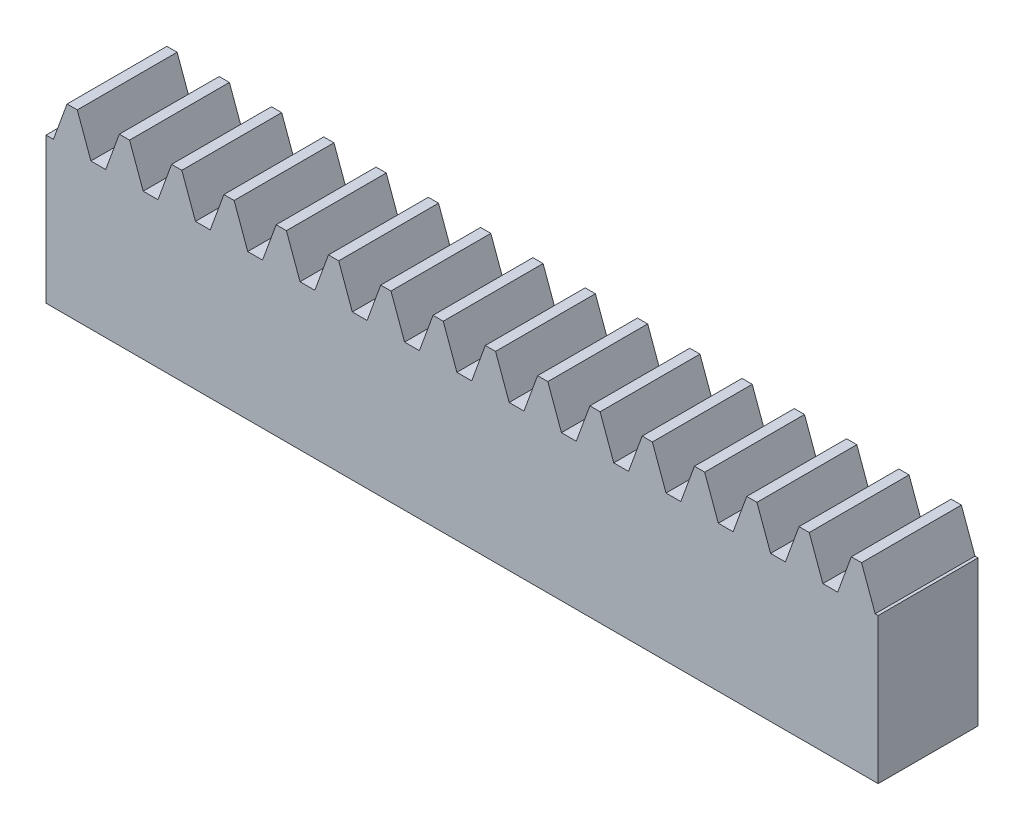
SolidWorks part; units mm, degrees
extrude "Blank" add sketch "BlankSke" against normal blind 6
sketch "BlankSke" plane through (0, 0, 0) normal (0, 0, 1) x (1, 0, 0)
  line L1 (0, 0) -> (50, 0)
  line L2 (0, 0) -> (0, 11)
  line L3 (0, 11) -> (50, 11)
  line L4 (50, 0) -> (50, 11)
  dimension "Length" = 50
  dimension "Blank_height" = 11
ref_plane "Plane1" through (0, 0, 0) normal (0, 0, 1) x (1, 0, 0)
ref_plane "Plane2" through (0, 0, 0) normal (0, 1, 0) x (1, 0, 0)
ref_plane "Plane3" through (0, 0, 0) normal (1, 0, 0) x (0, 0, -1)
sketch "HoldingSke" plane through (0, 0, 0) normal (0, 1, 0) x (1, 0, 0)
  line L0 (0, 0) -> (0.1392, 0.9903)
  line L1 (-15, 0) -> (100, 0) construction
  line L2 (0, 0) -> (-2.1039, 2.3779)
  line L3 (0, 0) -> (-11.863, 4.5341)
  line L4 (0, 0) -> (8.2587, 2.5249)
  line L5 (0, 0) -> (-23.7986, -8.8762)
  line L6 (0, 0) -> (-10.5278, -7.1032)
  line L9 (-71.009, 38.7566) -> (-24.0243, 55.8576)
  line L10 (-76.2, 3.3779) -> (-66.2, 3.3779)
  line L11 (0, 0) -> (-6, 0)
  line L12 (-76.2, 101.6) -> (-76.162, 101.6)
  line L13 (24.9733, 27.94) -> (52.9518, 28.4284)
  line L14 (24.9733, 27.94) -> (24.9743, 27.94)
  line L15 (24.9733, 27.94) -> (100.4006, 29.5858)
  circle A0 centre (0, 0) radius 19.05
  circle A1 centre (0, 0) radius 5
  circle A2 centre (0, 0) radius 12.7
  dimension "MPH" = 10
  dimension "Diameter" = 38.1
  dimension "Num_teeth" = 17
  dimension "Pitch" = 1
  dimension "Show_teeth" = 998
  dimension "Thickness" = 12.7
  dimension "Ap" = 20
  dimension "Pitch_height" = 10
  dimension "Width" = 6
  dimension "Backlash" = 0.038
  dimension "Addendum_fac" = 1
  dimension "Dedendum_fac" = 1.25
  dimension "Clearance_fac" = 0.25
  dimension "Dedendum_add" = 0.001
  dimension "Length" = 50
  dimension "Module" = 1
sketch "TooCutSkeIll" plane through (0, 0, 0) normal (0, 0, 1) x (1, 0, 0)
  line L0 (-1.2538, 10.9737) -> (-0.5045, 8.9152)
  line L1 (-0.2687, 8.75) -> (0.2687, 8.75)
  line L2 (0.5045, 8.9152) -> (1.2538, 10.9737)
  line L3 (50, 11) -> (0, 11) construction
  line L4 (0, 0) -> (0, 64.897) construction
  line L5 (-13.208, 10) -> (12.954, 10) construction
  line L6 (0, 0) -> (50, 0) construction
  line L7 (0.8994, 10) -> (0.8994, 48.7463) construction
  line L8 (-0.8994, 10) -> (-0.8994, 48.7463) construction
  line L9 (1.2914, 11) -> (1.2914, 11.0254)
  line L10 (-1.2914, 11) -> (-1.2914, 11.0254)
  line L11 (-1.2914, 11.0254) -> (1.2914, 11.0254)
  arc A0 (0.2687, 8.75) -> (0.5045, 8.9152) centre (0.2687, 9.001) ccw
  arc A1 (-0.5045, 8.9152) -> (-0.2687, 8.75) centre (-0.2687, 9.001) ccw
  arc A2 (1.2914, 11) -> (1.2538, 10.9737) centre (1.2914, 10.96) ccw
  arc A3 (-1.2538, 10.9737) -> (-1.2914, 11) centre (-1.2914, 10.96) ccw
  dimension "Pitch_height" = 10
  dimension "Addendum_plus" = 1.0254
  dimension "Pressure_angle" = 20
  dimension "Gap_width" = 1.7988
  dimension "Dedendum" = 1.25
extrude "ToothCutIll" [suppressed] cut sketch "TooCutSkeIll" against normal through all
sketch "TooCutSkeSim" plane through (0, 0, 0) normal (0, 0, 1) x (1, 0, 0)
  line L0 (0.4444, 8.75) -> (-0.4444, 8.75)
  line L1 (1.2726, 11.0254) -> (0.4444, 8.75)
  line L2 (0, 17.4625) -> (0, 53.467) construction
  line L3 (1.2726, 11.0254) -> (-1.2726, 11.0254)
  line L6 (-1.2726, 11.0254) -> (-0.4444, 8.75)
  line L9 (-0.8994, 10) -> (0.8994, 10) construction
  line L10 (0, 0) -> (50, 0) construction
  line L11 (0.8994, 10) -> (0.8994, 53.467) construction
  line L12 (-0.8994, 10) -> (-0.8994, 53.467) construction
  dimension "Pitch_height" = 10
  dimension "Addendum_plus" = 1.0254
  dimension "Pressure_angle" = 20
  dimension "Gap_width" = 1.7988
  dimension "Dedendum" = 1.25
extrude "ToothCutSim" cut sketch "TooCutSkeSim" against normal through all
pattern_linear "TeethCuts" count 17 spacing 3.1416 along (1, 0, 0) of "ToothCutIll", "ToothCutSim"
equation "' \"Module@HoldingSke\" = 6.35"
equation "' \"Num_teeth@HoldingSke\" = 12"
equation "' \"Ap@HoldingSke\" =  20"
equation "' \"Ap@HoldingSke\" = 20"
equation "' \"Width@HoldingSke\" = 0.25 * 25.4"
equation "' \"Show_teeth@HoldingSke\" = 500"
equation "' \"Backlash@HoldingSke\" = 0.009 * 25.4"
equation "' \"Addendum_fac@HoldingSke\" = 1.0"
equation "' \"Dedendum_fac@HoldingSke\" = 1.25"
equation "' \"Dedendum_add@HoldingSke\" = 0.00005 * 25.4"
equation "' \"Clearance_fac@HoldingSke\" = 0.25"
equation "' \"Pitch_height@HoldingSke\" = 1 * 25.4"
equation "' \"Length@HoldingSke\" = 4.71 * 25.4"
equation "\"Pitch@HoldingSke\" = 1 / \"Module@HoldingSke\""
equation "\"MPH@HoldingSke\" = \"Dedendum_fac@HoldingSke\" / \"Pitch@HoldingSke\" + 2 * \"Dedendum_add@HoldingSke\" + 0.002 * 25.4"
equation "\"MPH@HoldingSke\" = ((sgn( \"MPH@HoldingSke\" - \"Pitch_height@HoldingSke\")+1)*( \"MPH@HoldingSke\" - \"Pitch_height@HoldingSke\"))/2 + \"Pitch_height@HoldingSke\""
equation "\"Blank_height@BlankSke\" = \"Pitch_height@HoldingSke\" + \"Addendum_fac@HoldingSke\"  / \"Pitch@HoldingSke\" "
equation "\"Length@BlankSke\" =  \"Length@HoldingSke\""
equation "\"Face_width@Blank\" = \"Width@HoldingSke\""
equation "\"Pressure_angle@TooCutSkeIll\" = \"Ap@HoldingSke\""
equation "\"Addendum_plus@TooCutSkeIll\" =  \"Addendum_fac@HoldingSke\"  / \"Pitch@HoldingSke\" + 0.001 *25.4"
equation "\"Dedendum@TooCutSkeIll\" = \"Dedendum_fac@HoldingSke\"  / \"Pitch@HoldingSke\""
equation "\"Pitch_height@TooCutSkeIll\" =  \"MPH@HoldingSke\""
equation "\"Gap_width@TooCutSkeIll\" = 3.14159265 / 2 / \"Pitch@HoldingSke\" + 6 * \"Backlash@HoldingSke\""
equation "\"Pressure_angle@TooCutSkeSim\" = \"Ap@HoldingSke\""
equation "\"Addendum_plus@TooCutSkeSim\" =  \"Addendum_fac@HoldingSke\"  / \"Pitch@HoldingSke\" + 0.001 * 25.4"
equation "\"Dedendum@TooCutSkeSim\" = \"Dedendum_fac@HoldingSke\"  / \"Pitch@HoldingSke\""
equation "\"Pitch_height@TooCutSkeSim\" =  \"MPH@HoldingSke\""
equation "\"Gap_width@TooCutSkeSim\" = 3.14159265 / 2 / \"Pitch@HoldingSke\" + 6 * \"Backlash@HoldingSke\""
equation "\"Root_fillet@TooCutSkeIll\" = \"Clearance_fac@HoldingSke\" / \"Pitch@HoldingSke\" + \"Dedendum_add@HoldingSke\""
equation "\"Break_rad@TooCutSkeIll\" = 0.02 / \"Pitch@HoldingSke\" * 2"
equation "\"Linear_pitch@TeethCuts\" = 3.14159265 / \"Pitch@HoldingSke\""
equation "\"Num_teeth@HoldingSke\" = int( ( \"Length@HoldingSke\" + 0 ) / (3.14159265 / \"Pitch@HoldingSke\")) + 0.9999  + 1"
equation " \"Num_teeth@TeethCuts\" = int( \"Show_teeth@HoldingSke\" ) + 1"
equation " \"Num_teeth@TeethCuts\" = ((sgn( \"Num_teeth@TeethCuts\" - \"Num_teeth@HoldingSke\" )-1)*( \"Num_teeth@TeethCuts\" - \"Num_teeth@HoldingSke\" ))/-2+ \"Num_teeth@HoldingSke\""
equation " \"Num_teeth@TeethCuts\" = ((sgn( \"Num_teeth@TeethCuts\" - 2.0)+1)*( \"Num_teeth@TeethCuts\" - 2.0))/2 +2.0"
